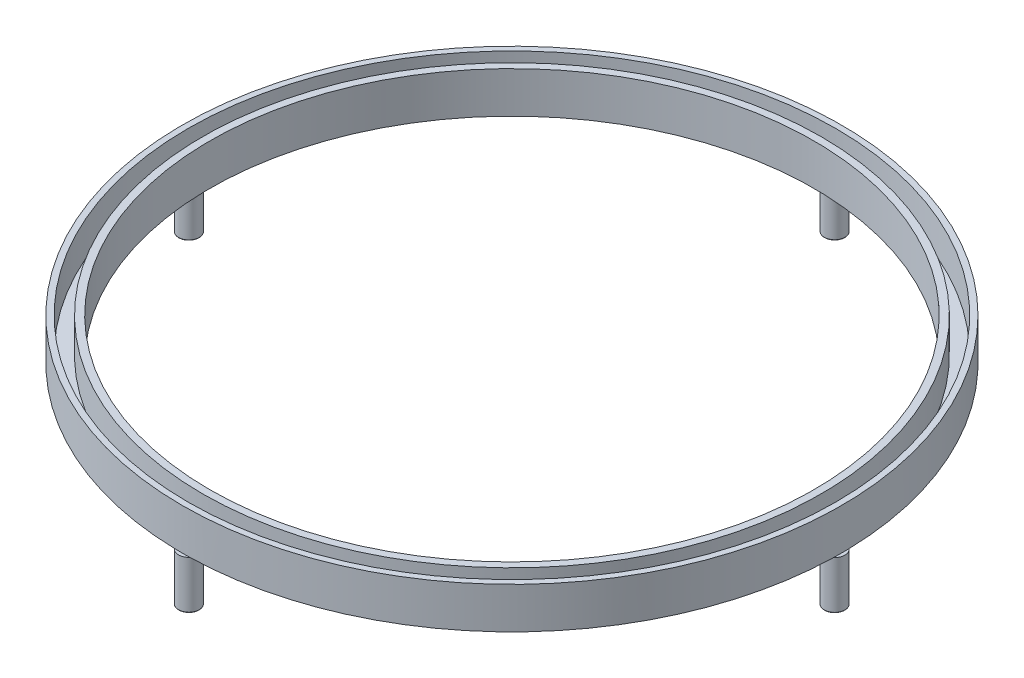
SolidWorks part; units mm, degrees
ref_plane "Front Plane" through (0, 0, 0) normal (0, 0, 1) x (1, 0, 0)
ref_plane "Top Plane" through (0, 0, 0) normal (0, 1, 0) x (1, 0, 0)
ref_plane "Right Plane" through (0, 0, 0) normal (1, 0, 0) x (0, 0, -1)
sketch "Sketch1" plane through (0, 0, 0) normal (0, 1, 0) x (1, 0, 0)
  circle A0 centre (0, 0) radius 48
  circle A1 centre (0, 0) radius 44
  dimension "D1" = 96
  dimension "D2" = 88
extrude "Boss-Extrude1" add sketch "Sketch1" along normal blind 6 contours A0 | A1
sketch "Sketch2" plane through (0, 0, 0) normal (0, 1, 0) x (1, 0, 0)
  circle A0 centre (0, 0) radius 47.15
  circle A1 centre (0, 0) radius 45.05
  dimension "D1" = 90.1
  dimension "D2" = 94.3
extrude "Cut-Extrude3" cut sketch "Sketch2" along normal blind 10 from offset 1
sketch "Sketch3" plane through (0, 0, 0) normal (0, 1, 0) x (1, 0, 0)
  circle A0 centre (0, 47) radius 1.5
  circle A1 centre (47, 0) radius 1.5
  circle A2 centre (-0.0452, -47) radius 1.5
  circle A3 centre (-47, -0.0452) radius 1.5
  dimension "D2" = 47
  dimension "D1" = 47
  dimension "D3" = 47
  dimension "D5" = 3
  dimension "D6" = 3
  dimension "D7" = 3
  dimension "D8" = 3
  dimension "D4" = 47
  dimension "D9" = 66.468
  dimension "D10" = 66.5
  dimension "D11" = 66.5
extrude "Boss-Extrude2" add sketch "Sketch3" against normal blind 7
fillet "Fillet1" radius 0.1 4 edges at (47, -7, 1.5) (0, -7, -45.5) (-0.0452, -7, 48.5) (-47, -7, 1.5452)
